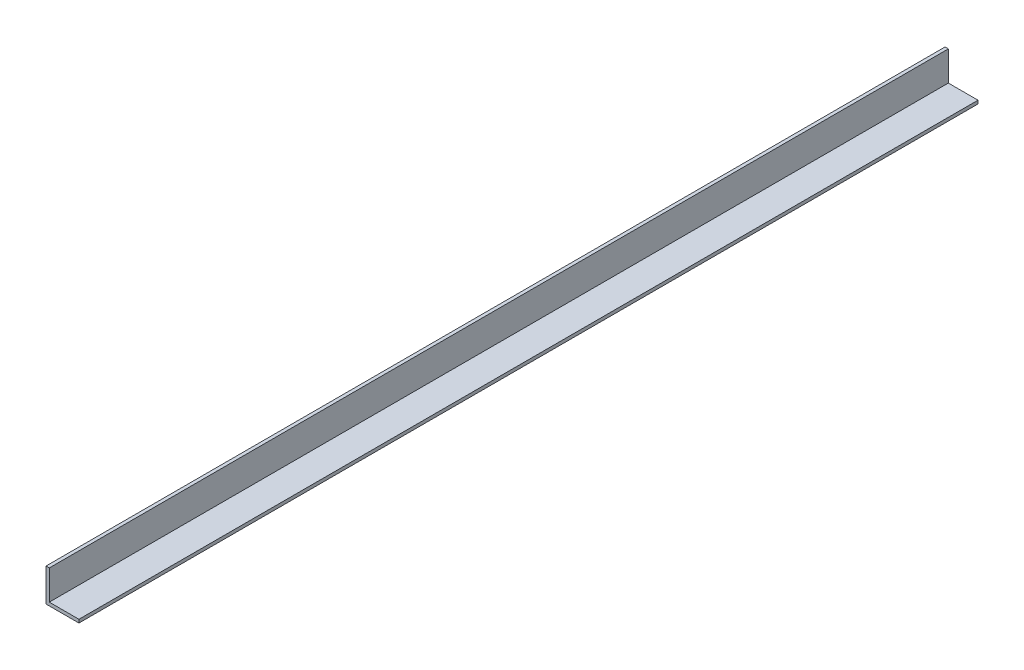
SolidWorks part; units mm, degrees
material "AISI 1020"
ref_plane "Front Plane" through (0, 0, 0) normal (0, 0, 1) x (1, 0, 0)
ref_plane "Top Plane" through (0, 0, 0) normal (0, 1, 0) x (1, 0, 0)
ref_plane "Right Plane" through (0, 0, 0) normal (1, 0, 0) x (0, 0, -1)
sketch "Sketch1" plane through (0, 0, 0) normal (0, 0, 1) x (1, 0, 0)
  line L1 (-14.5004, 9.9024) -> (5.4996, 9.9024)
  line L2 (-14.5004, 9.9024) -> (-14.5004, -10.0976)
  line L3 (-14.5004, -10.0976) -> (5.4996, -10.0976)
  line L4 (5.4996, 9.9024) -> (5.4996, -10.0976)
  line L5 (5.4996, 9.9024) -> (-12.5004, 9.9024)
  line L6 (5.4996, 9.9024) -> (5.4996, -8.0976)
  line L7 (5.4996, -8.0976) -> (-12.5004, -8.0976)
  line L8 (-12.5004, 9.9024) -> (-12.5004, -8.0976)
  dimension "D1" = 20
  dimension "D2" = 20
  dimension "D3" = 18
  dimension "D4" = 18
extrude "Boss-Extrude1" add sketch "Sketch1" against normal blind 546 contours L8 L1 L2 L3 L4 L7
